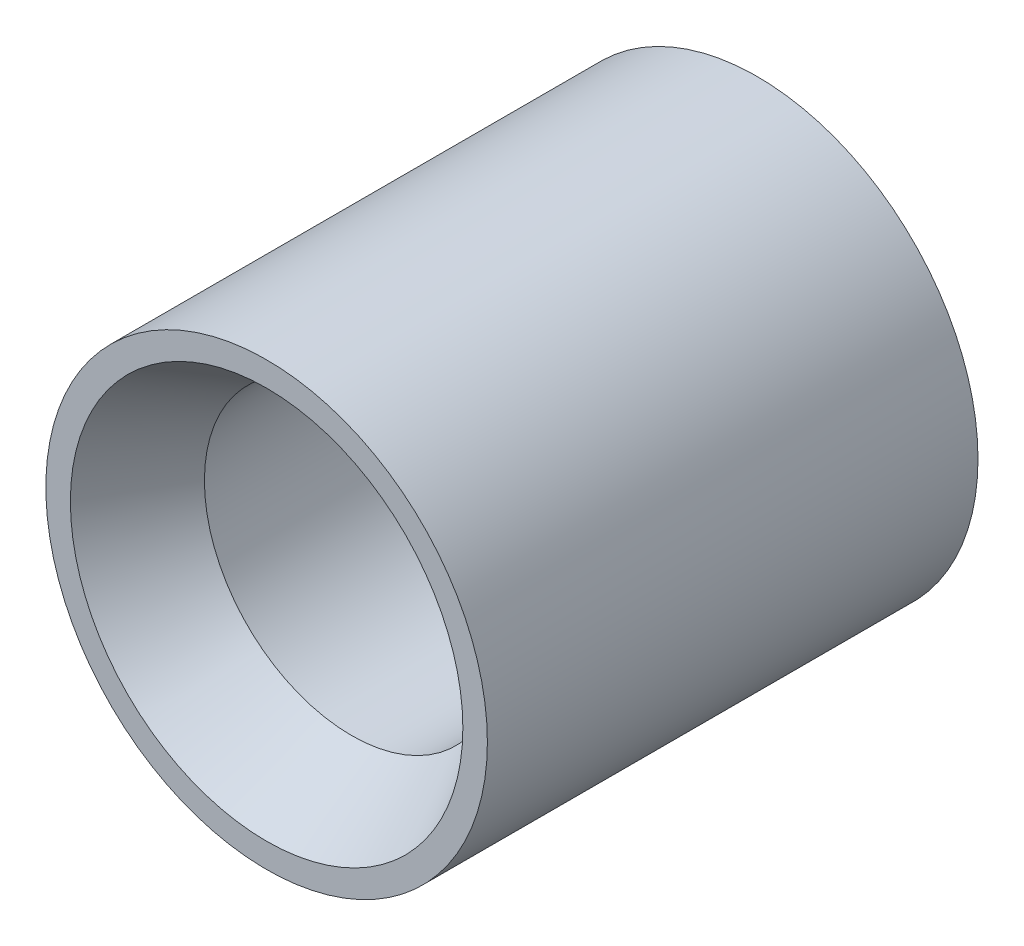
SolidWorks part; units mm, degrees
material "Alumina"
ref_plane "Front Plane" through (0, 0, 0) normal (0, 0, 1) x (1, 0, 0)
ref_plane "Top Plane" through (0, 0, 0) normal (0, 1, 0) x (1, 0, 0)
ref_plane "Right Plane" through (0, 0, 0) normal (1, 0, 0) x (0, 0, -1)
sketch "Sketch1" plane through (0, 0, 0) normal (0, 0, 1) x (1, 0, 0)
  circle A0 centre (0, -148.5737) radius 4.5
  circle A1 centre (0, 0) radius 4.5
  circle A2 centre (0, 0) radius 3
  dimension "D1" = 9
  dimension "D2" = 6
extrude "Boss-Extrude1" add sketch "Sketch1" along normal blind 10 contours A1 | A2
sketch "Sketch2" plane through (0, 0, 0) normal (0, 1, 0) x (1, 0, 0)
  line L0 (-4, -10) -> (0, -3.0718)
  line L1 (-4.5, -10) -> (4.5, -10) construction
  line L2 (0, -3.0718) -> (0, -10)
  line L3 (0, -10) -> (-4, -10)
  line L4 (0, 0) -> (0, -10) construction
  line L5 (3, 0) -> (-3, 0) construction
  point P4 (0, 0)
  point P6 (0, -10)
  point P8 (0.6577, -10.7183)
  dimension "D1" = 30
  dimension "D2" = 4
revolve "Cut-Revolve1" cut sketch "Sketch2" angle 360 about L4
